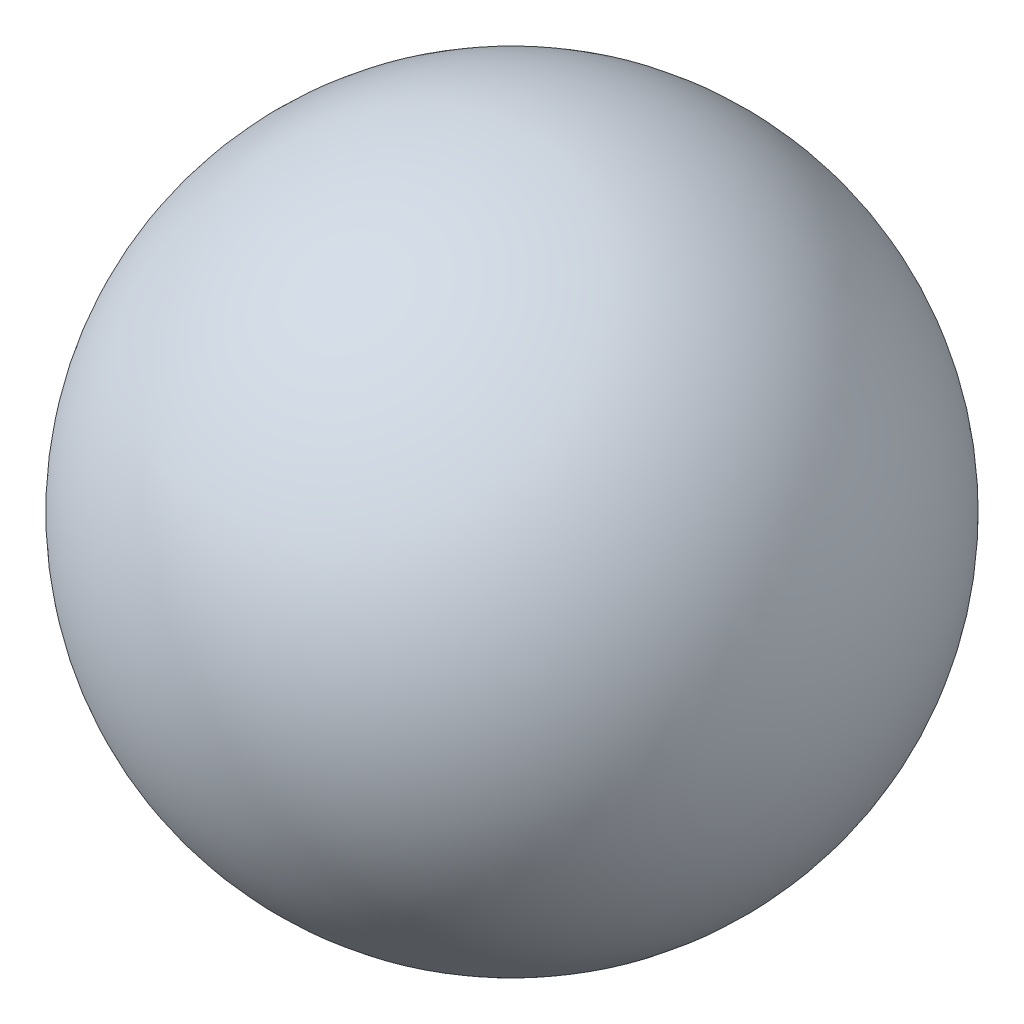
SolidWorks part; units mm, degrees
ref_plane "Front Plane" through (0, 0, 0) normal (0, 0, 1) x (1, 0, 0)
ref_plane "Top Plane" through (0, 0, 0) normal (0, 1, 0) x (1, 0, 0)
ref_plane "Right Plane" through (0, 0, 0) normal (1, 0, 0) x (0, 0, -1)
sketch "Sketch1" plane through (0, 0, 0) normal (0, 0, 1) x (1, 0, 0)
  line L0 (0, -203.2) -> (0, 203.2)
  arc A0 (0, -203.2) -> (0, 203.2) centre (0, 0) ccw
  dimension "D1" = 406.4
ref_axis "Axis1" through (0, -223.52, 0) along (0, 1, 0)
revolve "Revolve2" add sketch "Sketch1" angle 360 about axis through (0, -223.52, 0) along (0, 1, 0)
